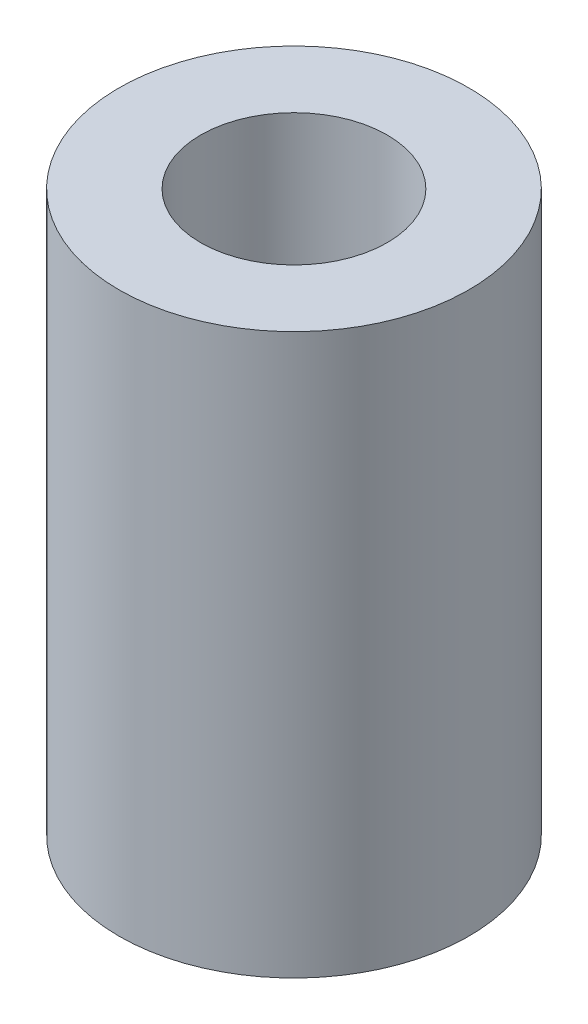
SolidWorks part; units mm, degrees
ref_plane "Plano frontal" through (0, 0, 0) normal (0, 0, 1) x (1, 0, 0)
ref_plane "Plano superior" through (0, 0, 0) normal (0, 1, 0) x (1, 0, 0)
ref_plane "Plano direito" through (0, 0, 0) normal (1, 0, 0) x (0, 0, -1)
sketch "Esboço1" plane through (0, 0, 0) normal (0, 1, 0) x (1, 0, 0)
  circle A0 centre (0, 0) radius 4
  circle A1 centre (0, 0) radius 7.5
  dimension "D1" = 8
  dimension "D2" = 15
extrude "Ressalto-extrusão1" add sketch "Esboço1" along normal blind 24
